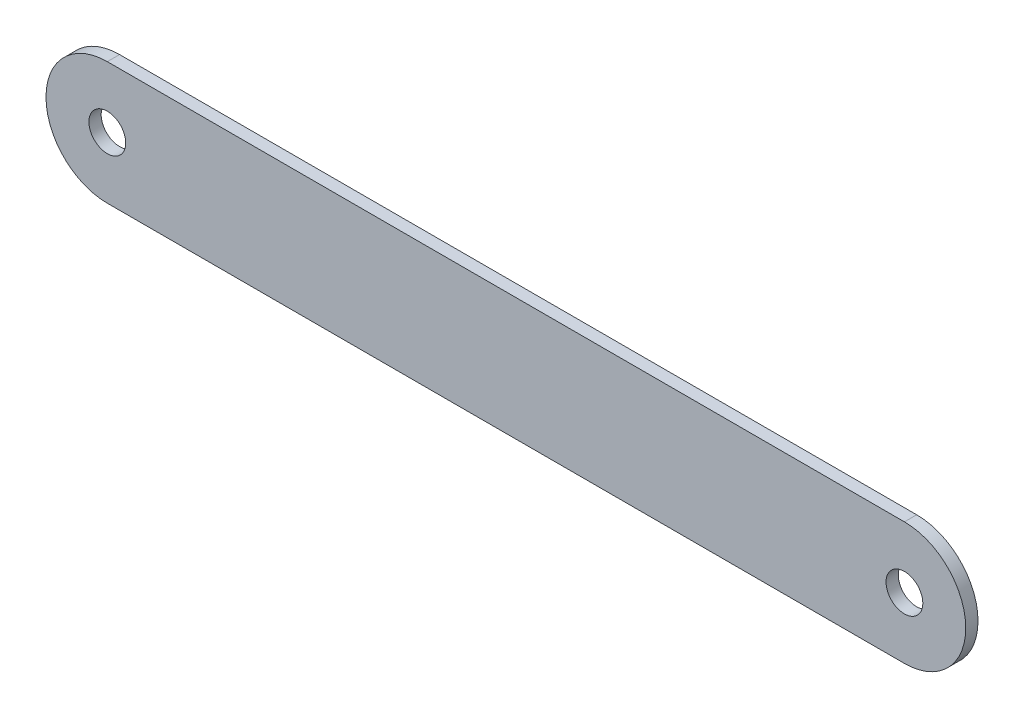
SolidWorks part; units mm, degrees
ref_plane "Ön Düzlem" through (0, 0, 0) normal (0, 0, 1) x (1, 0, 0)
ref_plane "Üst Düzlem" through (0, 0, 0) normal (0, 1, 0) x (1, 0, 0)
ref_plane "Sağ Düzlem" through (0, 0, 0) normal (1, 0, 0) x (0, 0, -1)
sketch "Çizim1" plane through (0, 0, 0) normal (0, 0, 1) x (1, 0, 0)
  line L0 (-65, 10) -> (65, -10) construction
  line L1 (-65, 10) -> (65, 10)
  line L2 (-65, 10) -> (-65, -10) construction
  line L3 (-65, -10) -> (65, -10)
  line L4 (65, 10) -> (65, -10) construction
  arc A0 (-65, 10) -> (-65, -10) centre (-65, 0) ccw
  arc A1 (65, -10) -> (65, 10) centre (65, 0) ccw
  circle A2 centre (-65, 0) radius 3
  circle A3 centre (65, 0) radius 3
  dimension "D1" = 130
  dimension "D2" = 20
extrude "Yükseklik-Ekstrüzyon1" add sketch "Çizim1" along normal blind 2
